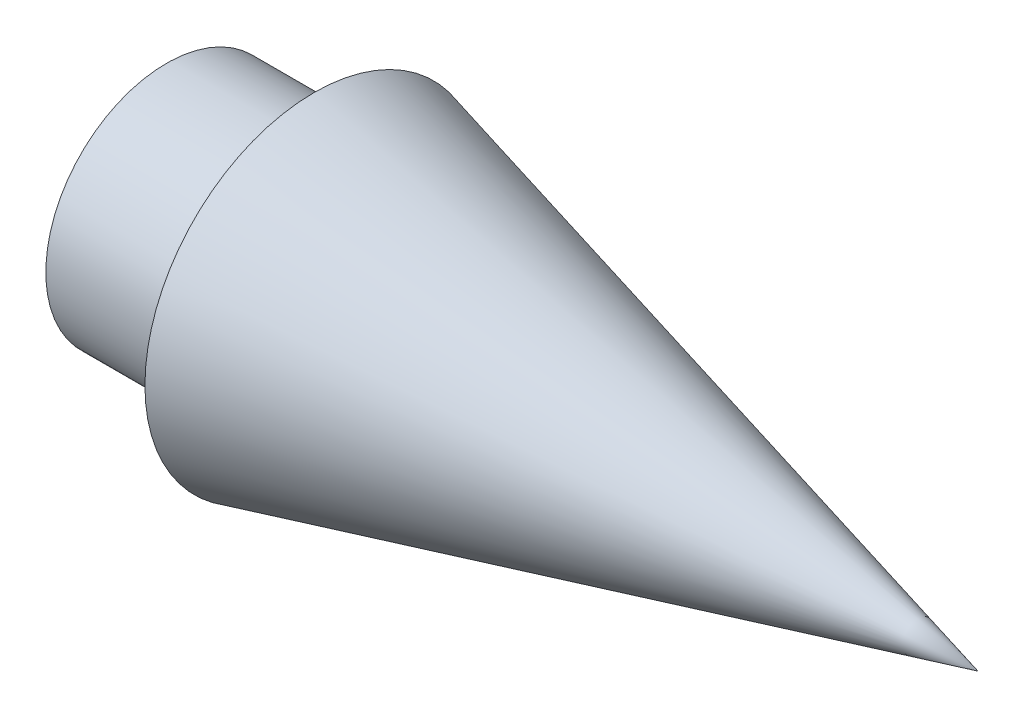
SolidWorks part; units mm, degrees
material "6061-T6 (SS)"
ref_plane "Front Plane" through (0, 0, 0) normal (0, 0, 1) x (1, 0, 0)
ref_plane "Top Plane" through (0, 0, 0) normal (0, 1, 0) x (1, 0, 0)
ref_plane "Right Plane" through (0, 0, 0) normal (1, 0, 0) x (0, 0, -1)
sketch "Sketch1" plane through (0, 0, 0) normal (0, 1, 0) x (1, 0, 0)
  line L0 (0, 10.3886) -> (0, 14.5579)
  line L1 (0, 14.5579) -> (57.15, 0)
  line L2 (57.15, 0) -> (0, 0)
  line L3 (0, 0) -> (-12.7, 0)
  line L4 (-12.7, 0) -> (-12.7, 10.3886)
  line L5 (-12.7, 10.3886) -> (0, 10.3886)
  dimension "D1" = 14.5579
  dimension "D2" = 57.15
  dimension "D3" = 12.7
  dimension "D4" = 10.3886
  dimension "D5" = 57.15
revolve "Revolve1" add sketch "Sketch1" angle 360 about L2
hole_wizard "1/4-20 Tapped Hole1" positions "Sketch3" profile "Sketch2" tap size "1/4-20" standard "ANSI Inch"
sketch "Sketch3" plane through (-12.7, 0, 0) normal (-1, 0, 0) x (0, 0, 1)
  point P3 (0, 0)
sketch "Sketch2" plane through (-12.7, 0, 0) normal (0, 1, 0) x (0, 0, 1)
  line L0 (0, 0) -> (0, 20.5838)
  line L1 (0, 20.5838) -> (2.5527, 19.05)
  line L2 (2.5527, 19.05) -> (2.5527, 0)
  line L5 (2.5527, 0) -> (0, 0)
  line L10 (0, 20.5838) -> (-2.5527, 19.05) construction
  line L11 (0, -6.35) -> (0, 107.95) construction
  dimension "Tap Drill Dia." = 5.1054
  dimension "Tap Drill Depth" = 19.05
  dimension "Drill Angle" = 118
cosmetic thread "Hole Thread1" parameters "D1"=12.7, "D2"=6.35
